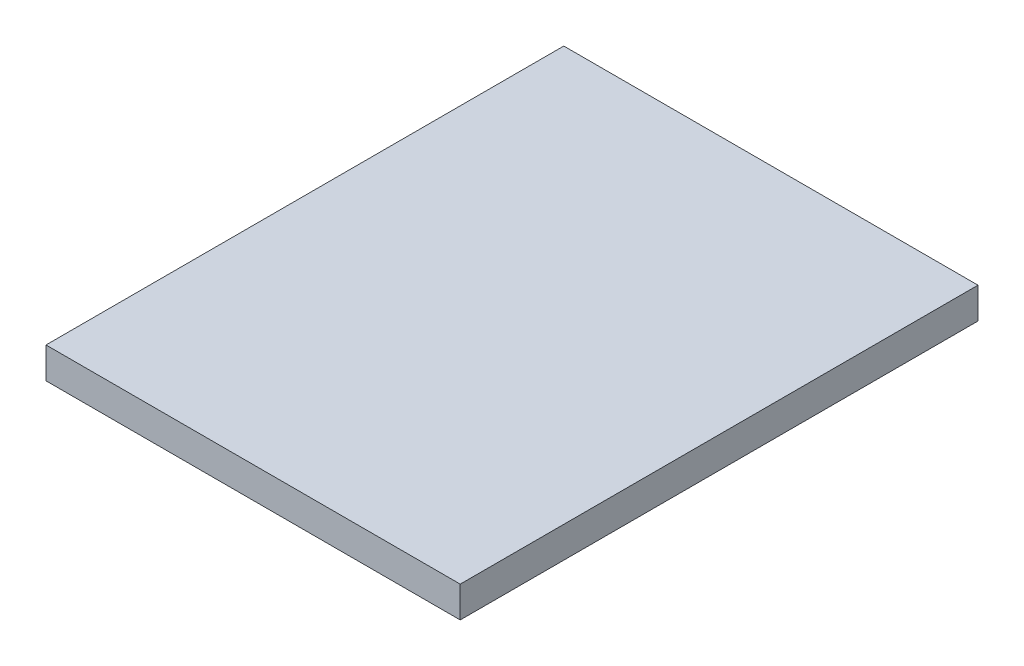
SolidWorks part; units mm, degrees
ref_plane "Front Plane" through (0, 0, 0) normal (0, 0, 1) x (1, 0, 0)
ref_plane "Top Plane" through (0, 0, 0) normal (0, 1, 0) x (1, 0, 0)
ref_plane "Right Plane" through (0, 0, 0) normal (1, 0, 0) x (0, 0, -1)
sketch "Sketch1" plane through (0, 0, 0) normal (0, 1, 0) x (1, 0, 0)
  line L1 (0, 0) -> (80, 0)
  line L2 (0, 0) -> (0, 100)
  line L3 (0, 100) -> (80, 100)
  line L4 (80, 0) -> (80, 100)
  dimension "D1" = 100
  dimension "D2" = 80
sketch "Sketch2" plane through (0, 0, 0) normal (0, 1, 0) x (1, 0, 0)
  line L0 (0, 0) -> (80, 0)
  line L1 (0, 0) -> (0, 100)
  line L2 (0, 100) -> (80, 100)
  line L3 (80, 0) -> (80, 100)
extrude "Boss-Extrude1" add sketch "Sketch2" along normal blind 6
